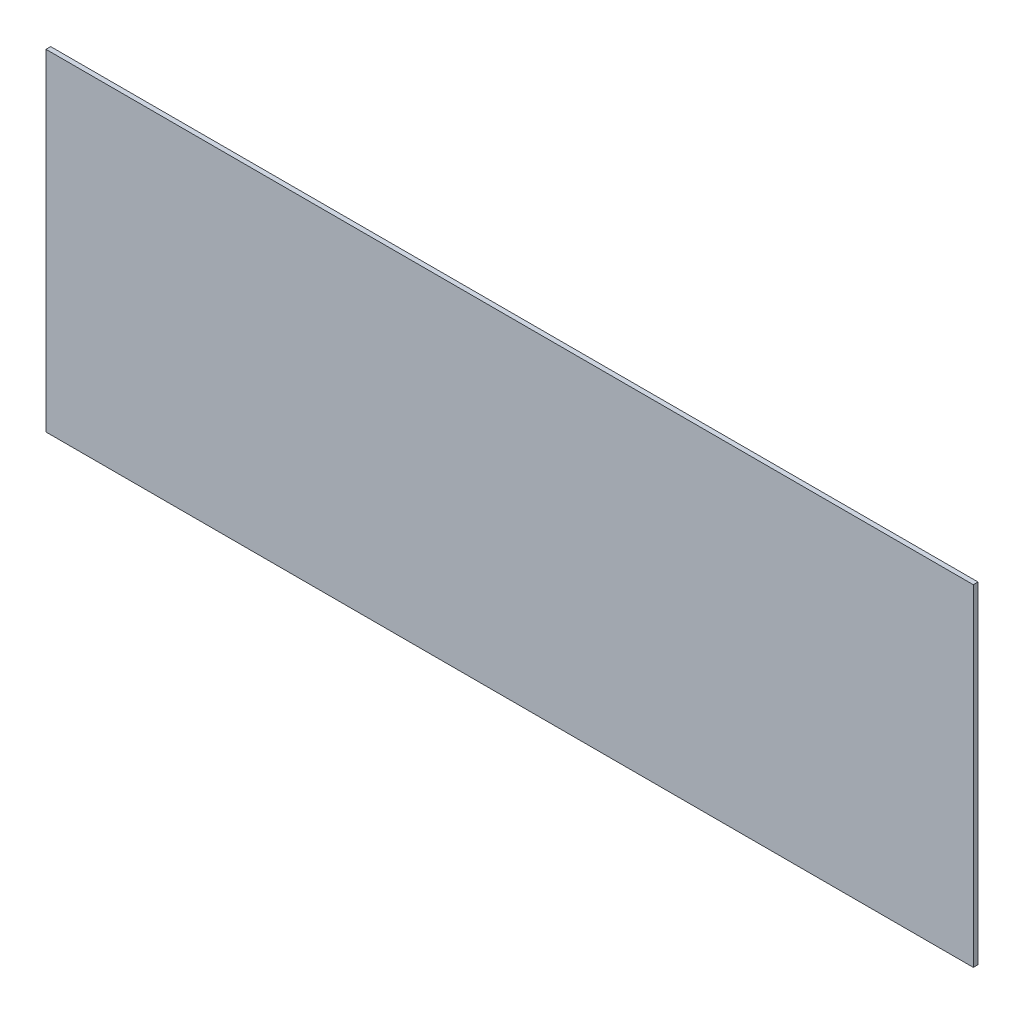
SolidWorks part; units mm, degrees
ref_plane "Alzado" through (0, 0, 0) normal (0, 0, 1) x (1, 0, 0)
ref_plane "Planta" through (0, 0, 0) normal (0, 1, 0) x (1, 0, 0)
ref_plane "Vista lateral" through (0, 0, 0) normal (1, 0, 0) x (0, 0, -1)
sketch "Croquis1" plane through (0, 0, 0) normal (0, 0, 1) x (1, 0, 0)
  line L1 (-98.2, -35.1) -> (98.2, -35.1)
  line L2 (-98.2, -35.1) -> (-98.2, 35.1)
  line L3 (-98.2, 35.1) -> (98.2, 35.1)
  line L4 (98.2, -35.1) -> (98.2, 35.1)
  line L5 (-98.2, -35.1) -> (98.2, 35.1) construction
  line L6 (-98.2, 35.1) -> (98.2, -35.1) construction
  point P0 (0, 0)
  dimension "D1" = 196.4
  dimension "D2" = 70.2
extrude "Saliente-Extruir1" add sketch "Croquis1" along normal blind 1
